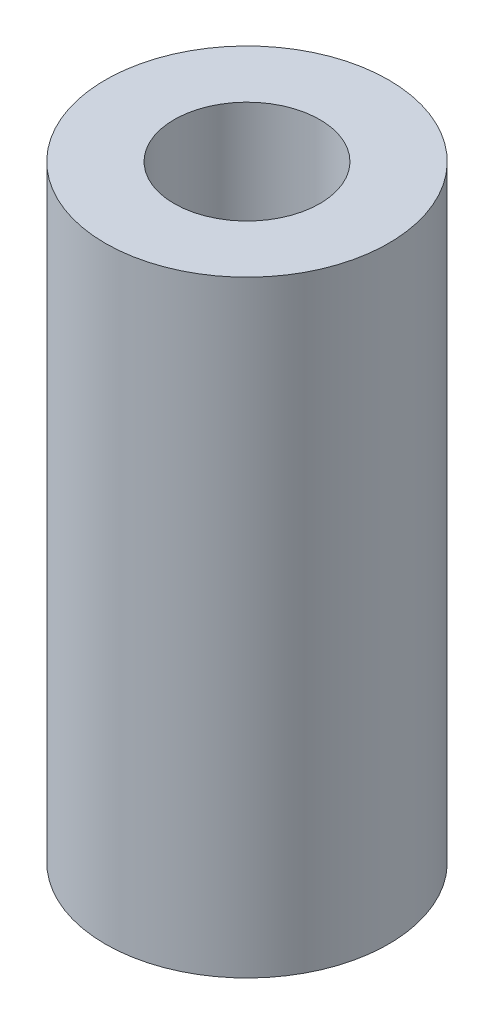
SolidWorks part; units mm, degrees
material "Nylon 101"
ref_plane "Front Plane" through (0, 0, 0) normal (0, 0, 1) x (1, 0, 0)
ref_plane "Top Plane" through (0, 0, 0) normal (0, 1, 0) x (1, 0, 0)
ref_plane "Right Plane" through (0, 0, 0) normal (1, 0, 0) x (0, 0, -1)
sketch "Sketch1" plane through (0, 0, 0) normal (0, 1, 0) x (1, 0, 0)
  circle A0 centre (0, 0) radius 3.5
  circle A1 centre (0, 0) radius 1.8
  dimension "D1" = 3.6
  dimension "D2" = 7
extrude "Boss-Extrude1" add sketch "Sketch1" along normal mid plane 15
